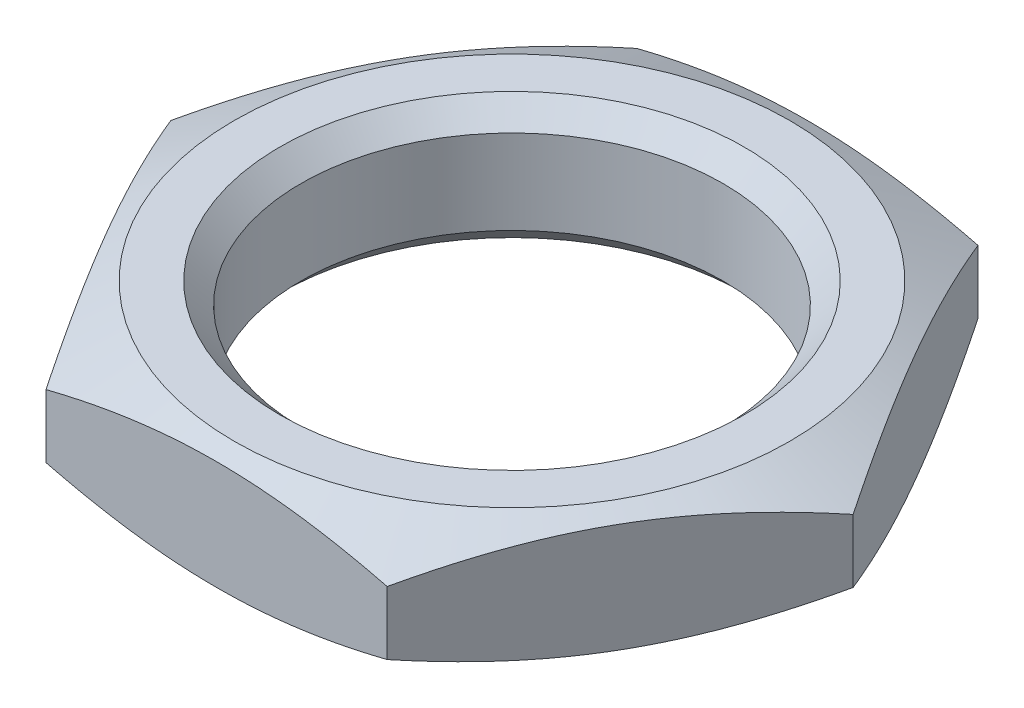
SolidWorks part; units mm, degrees
material "AISI 304"
ref_plane "Front Plane" through (0, 0, 0) normal (0, 0, 1) x (1, 0, 0)
ref_plane "Top Plane" through (0, 0, 0) normal (0, 1, 0) x (1, 0, 0)
ref_plane "Right Plane" through (0, 0, 0) normal (1, 0, 0) x (0, 0, -1)
sketch "Sketch1" plane through (0, 0, 0) normal (0, 1, 0) x (1, 0, 0)
  line L0 (0, -107.8058) -> (0, 5282.4859) construction
  line L1 (-107.8058, 0) -> (5282.4859, 0) construction
  line L3 (8.0829, 0) -> (4.0415, 7)
  line L4 (4.0415, 7) -> (-4.0415, 7)
  line L5 (-4.0415, 7) -> (-8.0829, 0)
  line L6 (-8.0829, 0) -> (-4.0415, -7)
  line L7 (-4.0415, -7) -> (4.0415, -7)
  line L8 (4.0415, -7) -> (8.0829, 0)
  circle A0 centre (0, 0) radius 5
  circle A1 centre (0, 0) radius 7 construction
  point P3 (8.0829, 0)
  dimension "D1" = 10
  dimension "D2" = 14
extrude "Boss-Extrude1" add sketch "Sketch1" along normal mid plane 3
sketch "Sketch2" plane through (0, 0, 0) normal (0, 0, 1) x (1, 0, 0)
  line L0 (-8.0829, 1.5) -> (-6.5829, 1.5)
  line L2 (-6.5829, 1.5) -> (-8.0829, 0.75)
  line L3 (-8.0829, 1.5) -> (-8.0829, -1.5) construction
  line L4 (-8.0829, 0.75) -> (-8.0829, 1.5)
  line L5 (-1000, 0) -> (49000, 0) construction
  line L6 (-8.0829, -0.75) -> (-8.0829, -1.5)
  line L7 (-6.5829, -1.5) -> (-8.0829, -0.75)
  line L8 (-8.0829, -1.5) -> (-6.5829, -1.5)
  line L9 (0, -1000) -> (0, 49000) construction
  line L10 (-8.0829, 1.5) -> (-4.0415, 1.5) construction
  point P3 (-6.5226, 1.5)
  point P15 (0, 0)
  dimension "D1" = 0.75
  dimension "D2" = 1.5
revolve "Cut-Revolve1" cut sketch "Sketch2" angle 360 about L9
chamfer "Chamfer1" distance 0.5 angle 45 2 edges at (0, -1.5, 5) (0, 1.5, 5)
